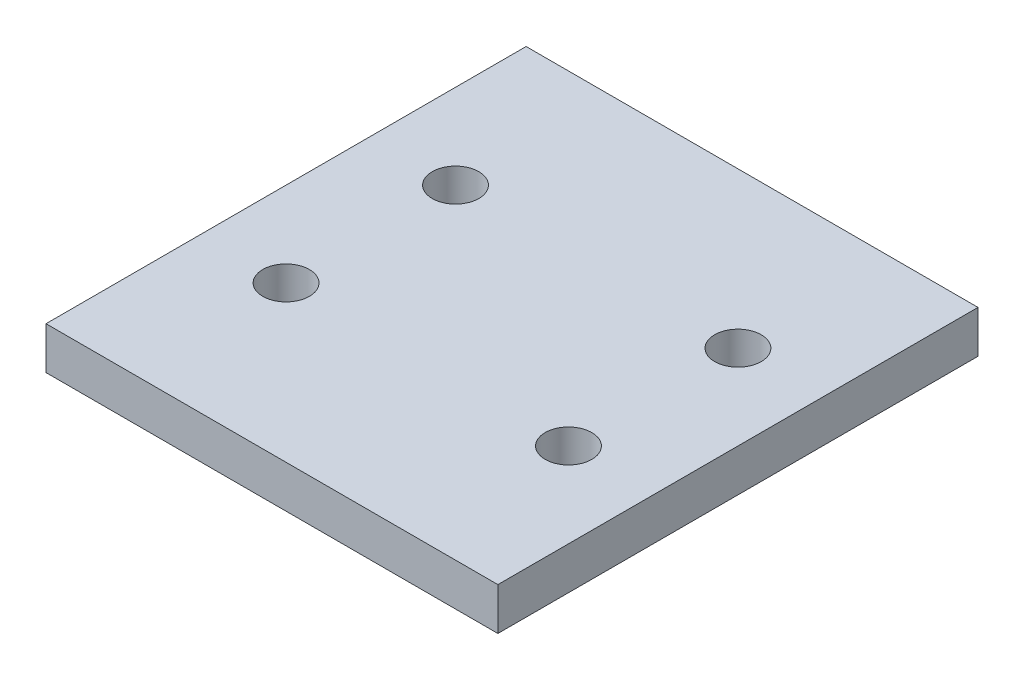
SolidWorks part; units mm, degrees
ref_plane "Front Plane" through (0, 0, 0) normal (0, 0, 1) x (1, 0, 0)
ref_plane "Top Plane" through (0, 0, 0) normal (0, 1, 0) x (1, 0, 0)
ref_plane "Right Plane" through (0, 0, 0) normal (1, 0, 0) x (0, 0, -1)
sketch "Sketch1" plane through (0, 0, 0) normal (0, 1, 0) x (1, 0, 0)
  line L0 (-16, 0) -> (16, 0) construction
  line L1 (-16, 17) -> (16, 17)
  line L2 (-16, 17) -> (-16, -17)
  line L3 (-16, -17) -> (16, -17)
  line L4 (16, 17) -> (16, -17)
  line L5 (-16, 17) -> (16, -17) construction
  line L6 (-16, -17) -> (16, 17) construction
  line L7 (0, 17) -> (0, -17) construction
  line L8 (-10, 17) -> (-10, -17) construction
  line L9 (10, 17) -> (10, -17) construction
  line L10 (-16, 6) -> (16, 6) construction
  line L11 (-16, -6) -> (16, -6) construction
  circle A0 centre (-10, 6) radius 1.65
  circle A1 centre (10, 6) radius 1.65
  circle A2 centre (-10, -6) radius 1.65
  circle A3 centre (10, -6) radius 1.65
  point P0 (0, 0)
  dimension "D7" = 3.3
  dimension "D8" = 3.3
  dimension "D9" = 3.3
  dimension "D10" = 3.3
  dimension "D1" = 32
  dimension "D2" = 34
  dimension "D3" = 10
  dimension "D4" = 10
  dimension "D5" = 6
  dimension "D6" = 6
  dimension "D11" = 12
extrude "Boss-Extrude1" add sketch "Sketch1" along normal blind 3
